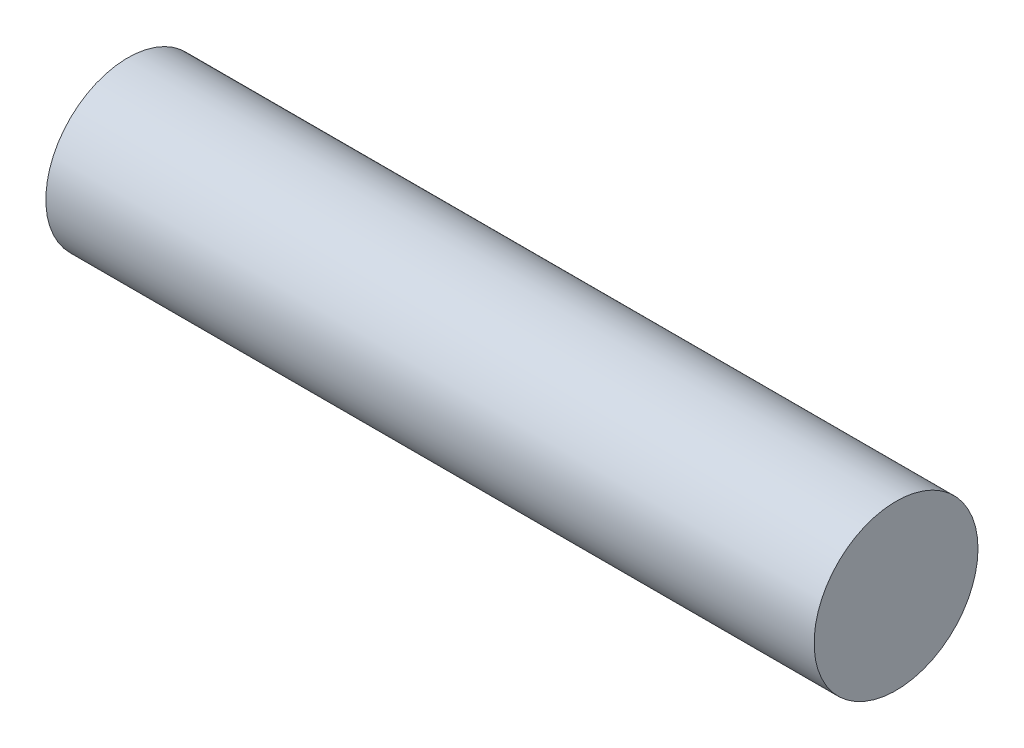
SolidWorks part; units mm, degrees
material "AISI 4130 Steel, annealed at 865C"
ref_plane "Front Plane" through (0, 0, 0) normal (0, 0, 1) x (1, 0, 0)
ref_plane "Top Plane" through (0, 0, 0) normal (0, 1, 0) x (1, 0, 0)
ref_plane "Right Plane" through (0, 0, 0) normal (1, 0, 0) x (0, 0, -1)
sketch "Sketch1" plane through (0, 0, 0) normal (1, 0, 0) x (0, 0, -1)
  circle A0 centre (0, 0) radius 4
  dimension "D1" = 8
extrude "Boss-Extrude1" add sketch "Sketch1" along normal blind 37.5
